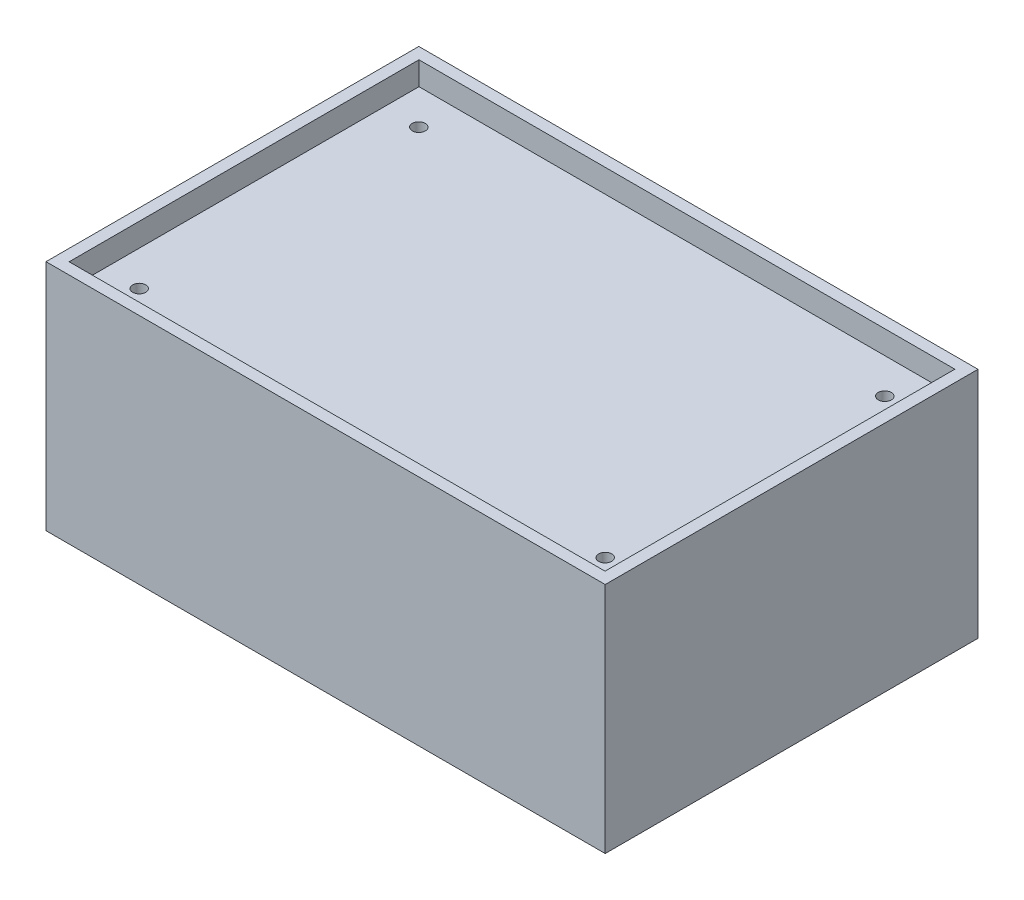
SolidWorks part; units mm, degrees
ref_plane "Front Plane" through (0, 0, 0) normal (0, 0, 1) x (1, 0, 0)
ref_plane "Top Plane" through (0, 0, 0) normal (0, 1, 0) x (1, 0, 0)
ref_plane "Right Plane" through (0, 0, 0) normal (1, 0, 0) x (0, 0, -1)
sketch "Sketch1" plane through (0, 0, 0) normal (0, 0, 1) x (1, 0, 0)
  line L1 (-76.2, 31.75) -> (76.2, 31.75)
  line L2 (-76.2, 31.75) -> (-76.2, -31.75)
  line L3 (-76.2, -31.75) -> (76.2, -31.75)
  line L4 (76.2, 31.75) -> (76.2, -31.75)
  line L5 (-76.2, 31.75) -> (76.2, -31.75) construction
  line L6 (-76.2, -31.75) -> (76.2, 31.75) construction
  point P0 (0, 0)
  dimension "D1" = 152.4
  dimension "D2" = 63.5
extrude "Boss-Extrude1" add sketch "Sketch1" against normal blind 101.6
sketch "Sketch3" plane through (0, 31.75, 0) normal (0, 1, 0) x (1, 0, 0)
  line L1 (-73.025, 98.47) -> (73.025, 98.47)
  line L2 (-73.025, 98.47) -> (-73.025, 3.13)
  line L3 (-73.025, 3.13) -> (73.025, 3.13)
  line L4 (73.025, 98.47) -> (73.025, 3.13)
  line L5 (-76.2, 101.6) -> (-76.2, 0) construction
  point P4 (0, 98.47)
  point P5 (-76.2, 50.8)
  point P7 (-73.025, 50.8)
  dimension "D1" = 146.05
  dimension "D2" = 95.34
extrude "Cut-Extrude1" cut sketch "Sketch3" against normal blind 6.35
mirror "Mirror1" about plane through (0, 0, 0) normal (0, 1, 0) of "Cut-Extrude1"
sketch "Sketch4" plane through (0, 25.4, 0) normal (0, 1, 0) x (1, 0, 0)
  line L0 (-73.025, 98.47) -> (-73.025, 3.13) construction
  circle A0 centre (63.5, 88.9) radius 1.78
  circle A1 centre (63.5, 12.7) radius 1.78
  circle A2 centre (-63.5, 88.9) radius 1.78
  circle A3 centre (-63.5, 12.7) radius 1.78
  point P8 (-73.025, 50.8)
  dimension "D1" = 3.56
  dimension "D2" = 76.2
  dimension "D3" = 127
  dimension "D4" = 63.5
  dimension "D5" = 38.1
extrude "Cut-Extrude2" cut sketch "Sketch4" against normal blind 10
